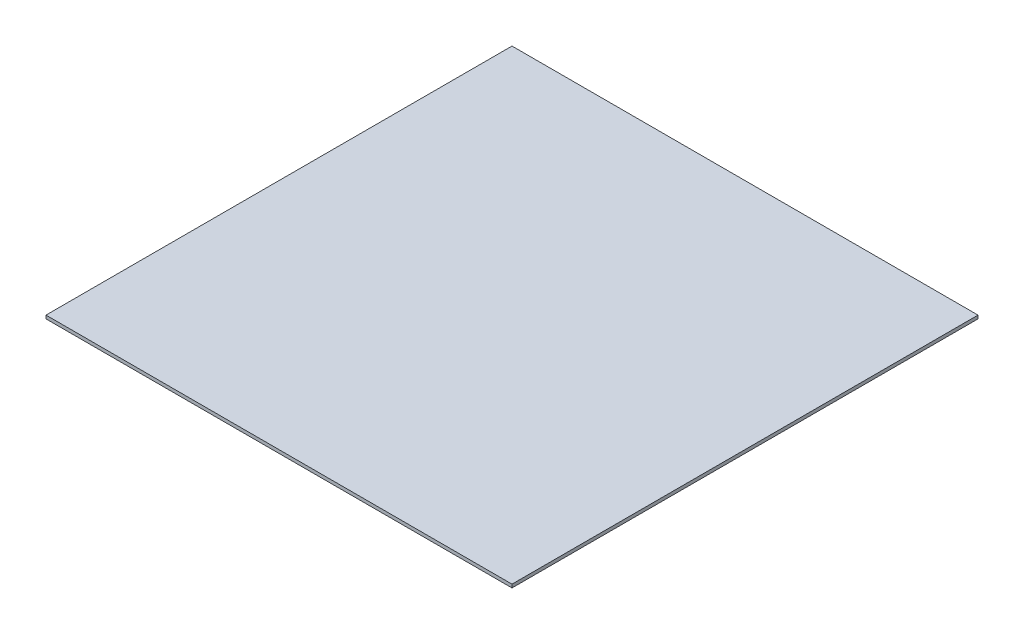
SolidWorks part; units mm, degrees
ref_plane "Front Plane" through (0, 0, 0) normal (0, 0, 1) x (1, 0, 0)
ref_plane "Top Plane" through (0, 0, 0) normal (0, 1, 0) x (1, 0, 0)
ref_plane "Right Plane" through (0, 0, 0) normal (1, 0, 0) x (0, 0, -1)
sketch "Sketch1" plane through (0, 0, 0) normal (0, 1, 0) x (1, 0, 0)
  line L0 (0, 0) -> (107.07, 0)
  line L1 (0, 0) -> (0, 107.07)
  line L2 (0, 107.07) -> (107.07, 107.07)
  line L3 (107.07, 107.07) -> (107.07, 0)
extrude "Boss-Extrude1" add sketch "Sketch1" along normal blind 0.762
scale "Scale2" bodies to scale 101 scale about centroid uniform scaling yes scale factor 0.75
